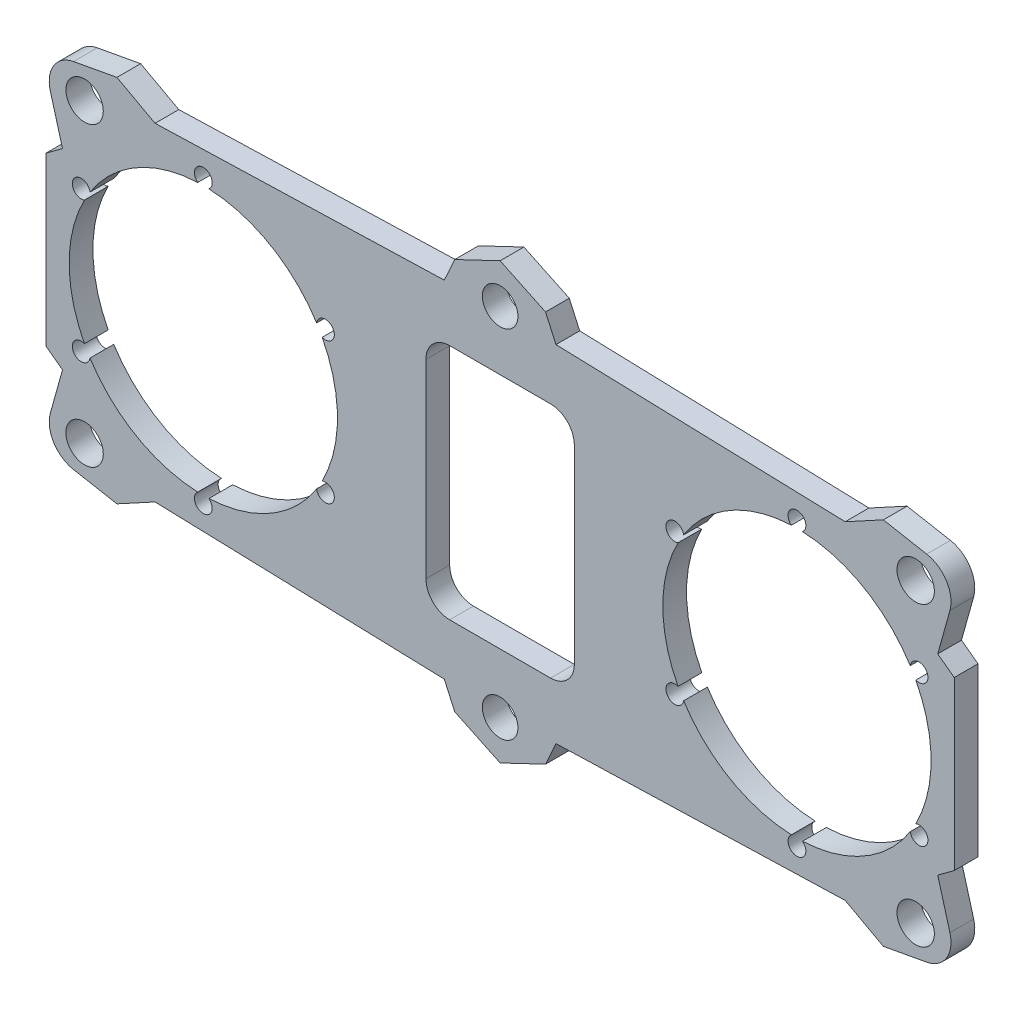
SolidWorks part; units mm, degrees
ref_plane "Front Plane" through (0, 0, 0) normal (0, 0, 1) x (1, 0, 0)
ref_plane "Top Plane" through (0, 0, 0) normal (0, 1, 0) x (1, 0, 0)
ref_plane "Right Plane" through (0, 0, 0) normal (1, 0, 0) x (0, 0, -1)
sketch "Sketch1" plane through (0, 0, 0) normal (0, 0, 1) x (1, 0, 0)
  line L0 (0, 36.6328) -> (-7.6473, 32.9908)
  line L1 (-7.6473, 32.9908) -> (-9.4053, 29.1042)
  line L2 (-9.4053, 29.1042) -> (-58.127, 27.6228)
  line L3 (-58.127, 27.6228) -> (-76.5, 14.0859)
  line L4 (-76.5, 14.0859) -> (-76.5, -14.0859)
  line L5 (-87.0431, 0) -> (20.0163, 0) construction
  line L6 (0, 32.2788) -> (0, 0) construction
  line L7 (76.5, 14.0859) -> (76.5, -14.0859)
  line L8 (58.127, 27.6228) -> (76.5, 14.0859)
  line L9 (9.4053, 29.1042) -> (58.127, 27.6228)
  line L10 (7.6473, 32.9908) -> (9.4053, 29.1042)
  line L11 (0, 36.6328) -> (7.6473, 32.9908)
  line L12 (0, -36.6328) -> (7.6473, -32.9908)
  line L13 (7.6473, -32.9908) -> (9.4053, -29.1042)
  line L14 (9.4053, -29.1042) -> (58.127, -27.6228)
  line L15 (58.127, -27.6228) -> (76.5, -14.0859)
  line L16 (-58.127, -27.6228) -> (-76.5, -14.0859)
  line L17 (-9.4053, -29.1042) -> (-58.127, -27.6228)
  line L18 (-7.6473, -32.9908) -> (-9.4053, -29.1042)
  line L19 (0, -36.6328) -> (-7.6473, -32.9908)
  circle A0 centre (0, 30) radius 3
  circle A1 centre (-50, 0) radius 22.6
  circle A2 centre (50, 0) radius 22.6
  circle A3 centre (0, -30) radius 3
  point P35 (76.5, 0)
  point P36 (-76.5, 0)
  dimension "D1" = 6
  dimension "D2" = 45.2
  dimension "D3" = 60
  dimension "D4" = 100
  dimension "D5" = 153
extrude "Boss-Extrude1" add sketch "Sketch1" along normal blind 4
sketch "Sketch2" plane through (0, 0, 4) normal (0, 0, 1) x (1, 0, 0)
  line L1 (8.5, 20) -> (-8.5, 20)
  line L2 (12.5, 16) -> (12.5, -16)
  line L3 (8.5, -20) -> (-8.5, -20)
  line L4 (-12.5, 16) -> (-12.5, -16)
  line L5 (12.5, 20) -> (-12.5, -20) construction
  line L6 (12.5, -20) -> (-12.5, 20) construction
  arc A1 (8.5, 20) -> (12.5, 16) centre (8.5, 16) cw
  arc A2 (12.5, -16) -> (8.5, -20) centre (8.5, -16) cw
  arc A3 (-8.5, -20) -> (-12.5, -16) centre (-8.5, -16) cw
  arc A4 (-8.5, 20) -> (-12.5, 16) centre (-8.5, 16) ccw
  point P0 (0, 0)
  dimension "D1" = 4
  dimension "D2" = 25
  dimension "D3" = 40
extrude "Cut-Extrude1" cut sketch "Sketch2" against normal through all
sketch "Sketch3" plane through (0, 0, 4) normal (0, 0, 1) x (1, 0, 0)
  line L0 (-58.127, 27.6228) -> (-64.5519, 31.11)
  line L1 (-58.127, 27.6228) -> (-76.5, 14.0859) construction
  line L2 (-64.5519, 31.11) -> (-77.2451, 28.7738)
  line L3 (-77.2451, 28.7738) -> (-73.717, 16.1363)
  line L4 (-73.717, 16.1363) -> (-58.127, 27.6228)
  line L5 (0, 0) -> (0, 46.5274) construction
  line L6 (73.717, 16.1363) -> (58.127, 27.6228)
  line L7 (77.2451, 28.7738) -> (73.717, 16.1363)
  line L8 (64.5519, 31.11) -> (77.2451, 28.7738)
  line L9 (58.127, 27.6228) -> (64.5519, 31.11)
  line L10 (0, 0) -> (-26.0239, 0) construction
  line L11 (58.127, -27.6228) -> (64.5519, -31.11)
  line L12 (64.5519, -31.11) -> (77.2451, -28.7738)
  line L13 (77.2451, -28.7738) -> (73.717, -16.1363)
  line L14 (73.717, -16.1363) -> (58.127, -27.6228)
  line L15 (-73.717, -16.1363) -> (-58.127, -27.6228)
  line L16 (-77.2451, -28.7738) -> (-73.717, -16.1363)
  line L17 (-64.5519, -31.11) -> (-77.2451, -28.7738)
  line L18 (-58.127, -27.6228) -> (-64.5519, -31.11)
  line L19 (-9.4053, 29.1042) -> (-58.127, 27.6228) construction
  circle A0 centre (-70, 25) radius 3.15
  circle A1 centre (70, 25) radius 3.15
  circle A2 centre (-70, -25) radius 3.15
  circle A3 centre (70, -25) radius 3.15
  dimension "D1" = 6.3
  dimension "D2" = 70
  dimension "D3" = 25
extrude "Boss-Extrude2" add sketch "Sketch3" against normal up to surface (4 mm away) up to face at (0, 0, 0)
fillet "Fillet1" radius 5 4 edges at (-77.2451, 28.7738, 2) (-77.2451, -28.7738, 2) (77.2451, -28.7738, 2) (77.2451, 28.7738, 2)
sketch "Sketch4" plane through (0, 0, 4) normal (0, 0, 1) x (1, 0, 0)
  line L0 (0, 48.5627) -> (0, -47.8194) construction
  circle A0 centre (-50, 0) radius 23.75 construction
  circle A1 centre (-50, 23.75) radius 1.5
  circle A2 centre (-70.5681, 11.875) radius 1.5
  circle A3 centre (-70.5681, -11.875) radius 1.5
  circle A4 centre (-50, -23.75) radius 1.5
  circle A5 centre (-29.4319, -11.875) radius 1.5
  circle A6 centre (-29.4319, 11.875) radius 1.5
  circle A7 centre (29.4319, 11.875) radius 1.5
  circle A8 centre (29.4319, -11.875) radius 1.5
  circle A9 centre (50, -23.75) radius 1.5
  circle A10 centre (70.5681, -11.875) radius 1.5
  circle A11 centre (70.5681, 11.875) radius 1.5
  circle A12 centre (50, 23.75) radius 1.5
  point P21 (-50, 0)
  point P31 (50, 0)
  dimension "D1" = 47.5
  dimension "D3" = 3
  dimension "D2" = 6
extrude "Cut-Extrude2" cut sketch "Sketch4" against normal through all
